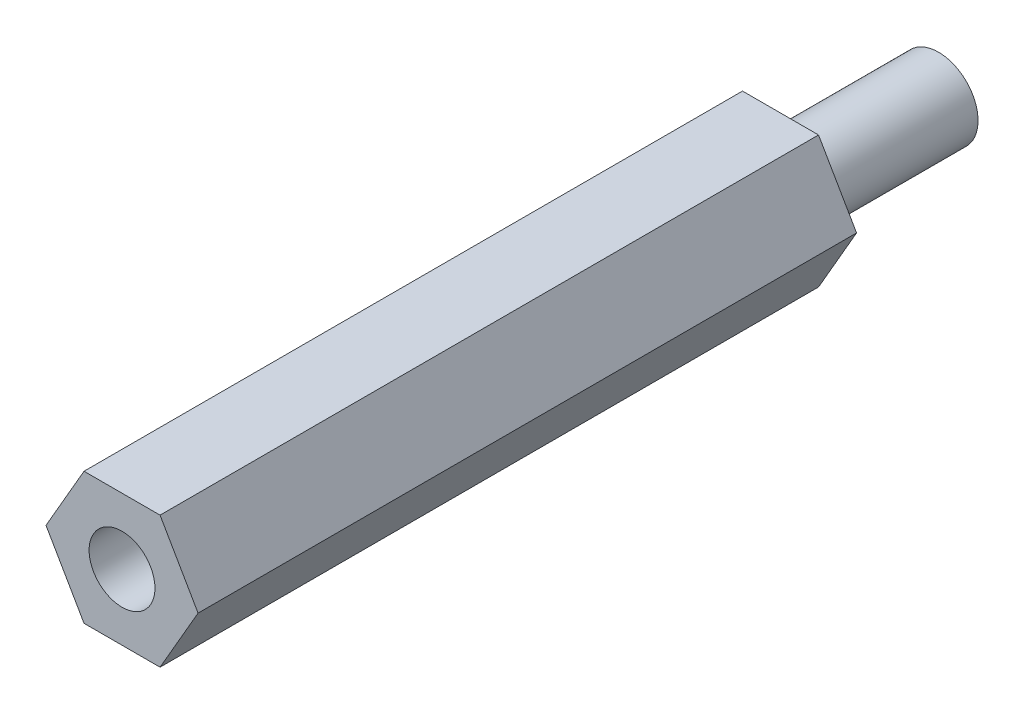
SolidWorks part; units mm, degrees
material "黃銅"
ref_plane "前基準面" through (0, 0, 0) normal (0, 0, 1) x (1, 0, 0)
ref_plane "上基準面" through (0, 0, 0) normal (0, 1, 0) x (1, 0, 0)
ref_plane "右基準面" through (0, 0, 0) normal (1, 0, 0) x (0, 0, -1)
sketch "草圖1" plane through (0, 0, 0) normal (0, 0, 1) x (1, 0, 0)
  line L1 (-1.4434, 2.5) -> (-2.8868, 0)
  line L2 (-2.8868, 0) -> (-1.4434, -2.5)
  line L3 (-1.4434, -2.5) -> (1.4434, -2.5)
  line L4 (1.4434, -2.5) -> (2.8868, 0)
  line L5 (2.8868, 0) -> (1.4434, 2.5)
  line L6 (1.4434, 2.5) -> (-1.4434, 2.5)
  circle A0 centre (0, 0) radius 2.5 construction
  dimension "D1" = 5
extrude "填料-伸長1" add sketch "草圖1" along normal blind 25
sketch "草圖4" plane through (0, 0, 0) normal (0, 0, -1) x (-1, 0, 0)
  circle A0 centre (0, 0) radius 1.5
  dimension "D1" = 3
extrude "填料-伸長2" add sketch "草圖4" along normal blind 6
hole_wizard "M3x0.5 螺紋孔1" positions "草圖2" profile "草圖3" tap size "M3x0.5" standard "Ansi Metric"
sketch "草圖2" plane through (0, 0, 25) normal (0, 0, 1) x (1, 0, 0)
  point P0 (0, 0)
sketch "草圖3" plane through (0, 0, 25) normal (1, 0, 0) x (0, -1, 0)
  line L0 (0, 0) -> (0, 8.2511)
  line L1 (0, 8.2511) -> (1.25, 7.5)
  line L2 (1.25, 7.5) -> (1.25, 0)
  line L5 (1.25, 0) -> (0, 0)
  line L10 (0, 8.2511) -> (-1.25, 7.5) construction
  line L11 (0, -6.35) -> (0, 107.95) construction
  dimension "螺孔鑽直徑" = 2.5
  dimension "螺孔鑽深度" = 7.5
  dimension "導頭角度" = 118
